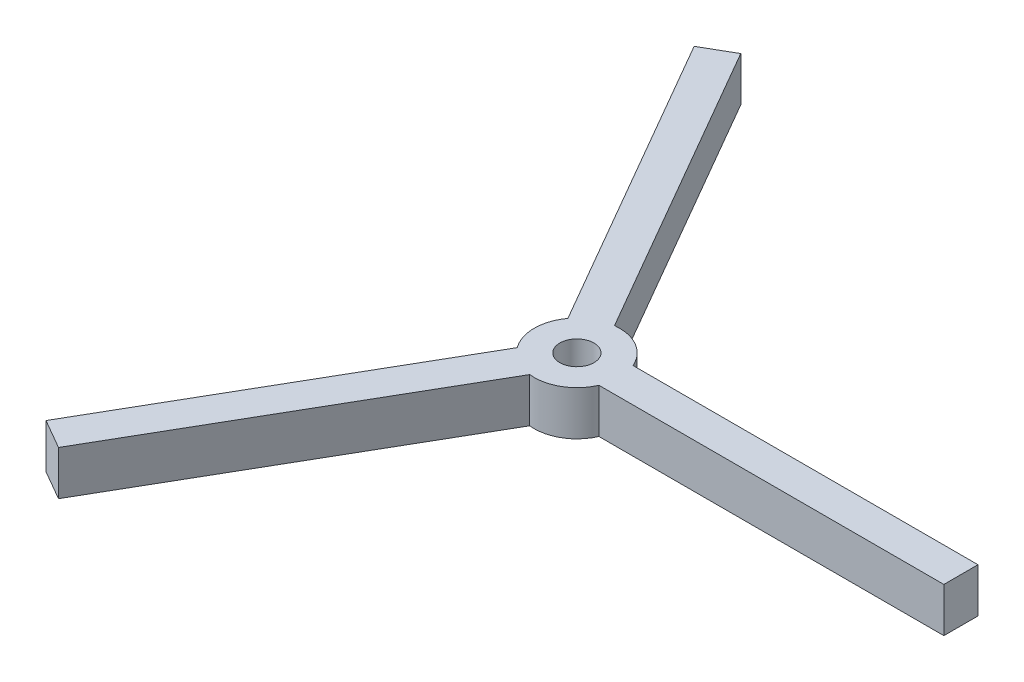
SolidWorks part; units mm, degrees
ref_plane "Front Plane" through (0, 0, 0) normal (0, 0, 1) x (1, 0, 0)
ref_plane "Top Plane" through (0, 0, 0) normal (0, 1, 0) x (1, 0, 0)
ref_plane "Right Plane" through (0, 0, 0) normal (1, 0, 0) x (0, 0, -1)
sketch "Sketch1" plane through (0, 0, 0) normal (0, 1, 0) x (1, 0, 0)
  circle A0 centre (0, 0) radius 6.35
  circle A1 centre (0, 0) radius 2.54
  dimension "D1" = 12.7
  dimension "D2" = 5.08
extrude "Boss-Extrude1" add sketch "Sketch1" along normal blind 6.604
ref_plane "Plane1" through (6.35, 0, 0) normal (1, 0, 0) x (0, 0, -1)
sketch "Sketch2" plane through (6.35, 0, 0) normal (1, 0, 0) x (0, 0, -1)
  line L0 (-6.35, 0) -> (6.35, 0) construction
  line L1 (-2.54, 0) -> (2.54, 0)
  line L2 (-2.54, 0) -> (-2.54, 6.604)
  line L3 (-2.54, 6.604) -> (2.54, 6.604)
  line L4 (2.54, 0) -> (2.54, 6.604)
  line L5 (6.35, 6.604) -> (-6.35, 6.604) construction
  dimension "D1" = 2.54
  dimension "D2" = 5.08
extrude "Boss-Extrude2" add sketch "Sketch2" along normal blind 50.8 and the other way up to surface
pattern_circular "CirPattern1" count 3 over 360 about axis through (0, 0, 0) along (0, 1, 0) of "Boss-Extrude2"
